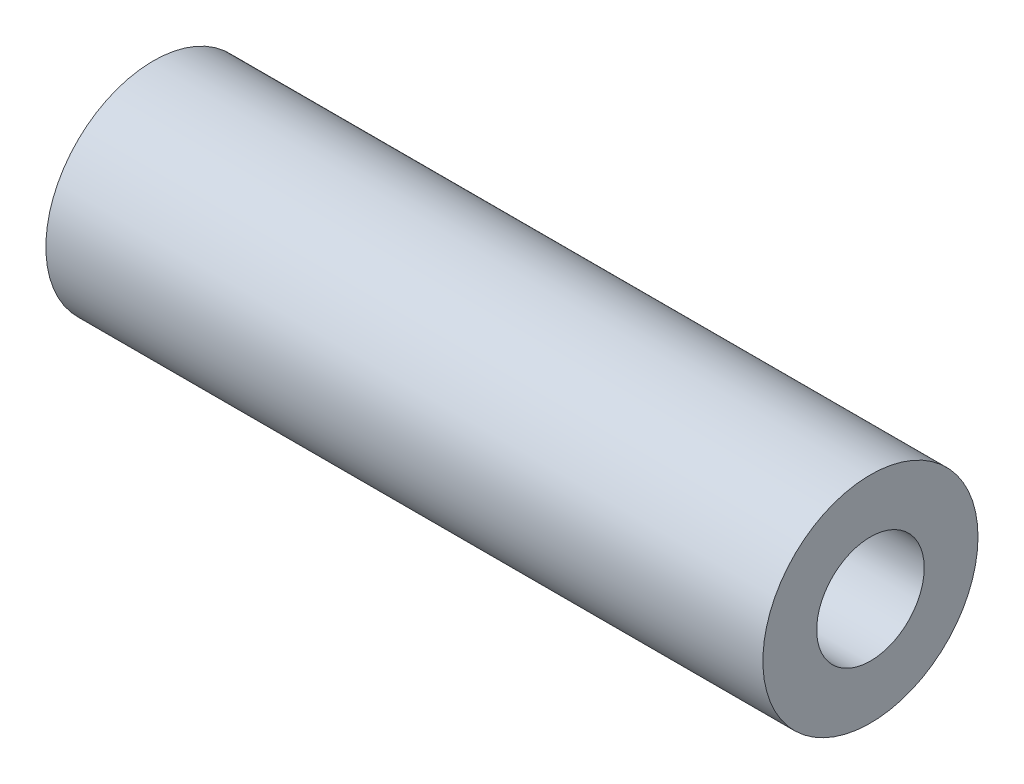
SolidWorks part; units mm, degrees
material "POLYURETHANE (11671)"
ref_plane "Front Plane" through (0, 0, 0) normal (0, 0, 1) x (1, 0, 0)
ref_plane "Top Plane" through (0, 0, 0) normal (0, 1, 0) x (1, 0, 0)
ref_plane "Right Plane" through (0, 0, 0) normal (1, 0, 0) x (0, 0, -1)
sketch "Sketch1" plane through (0, 0, 0) normal (1, 0, 0) x (0, 0, -1)
  circle A0 centre (0, 0) radius 9.525
  circle A1 centre (0, 0) radius 19.05
  dimension "D1" = 19.05
  dimension "D2" = 38.1
extrude "Boss-Extrude1" add sketch "Sketch1" along normal mid plane 127
